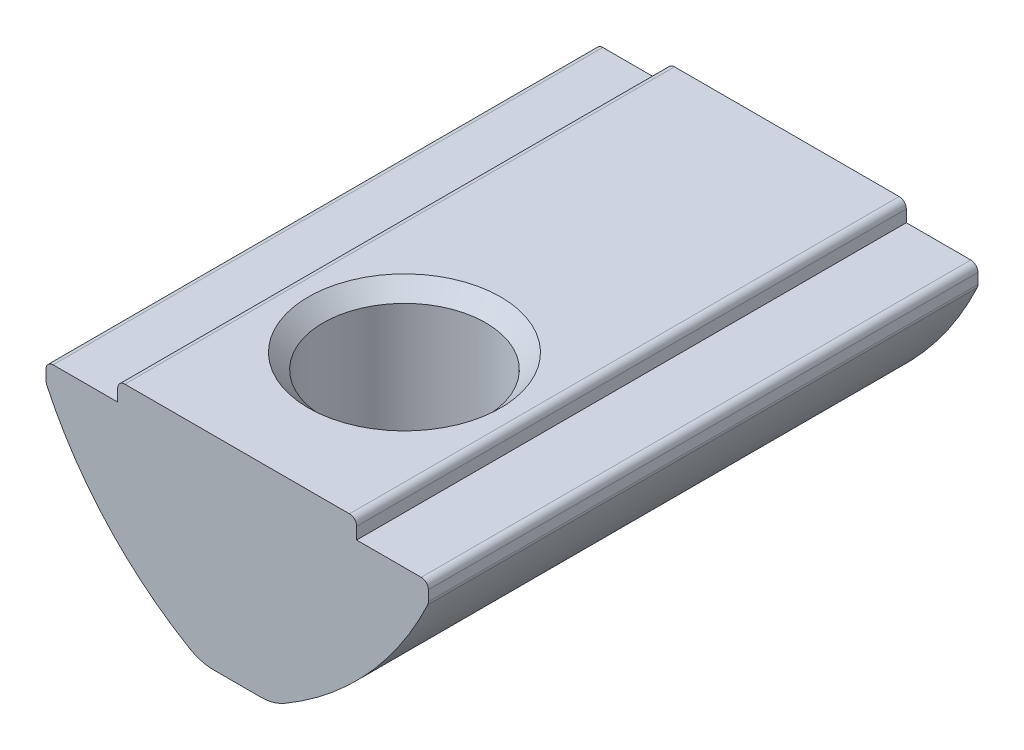
SolidWorks part; units mm, degrees
ref_plane "Спереди" through (0, 0, 0) normal (0, 0, 1) x (1, 0, 0)
ref_plane "Сверху" through (0, 0, 0) normal (0, 1, 0) x (1, 0, 0)
ref_plane "Справа" through (0, 0, 0) normal (1, 0, 0) x (0, 0, -1)
sketch "Эскиз1" plane through (0, 0, 0) normal (0, 0, 1) x (1, 0, 0)
  line L0 (-5, 0) -> (5, 0)
  line L5 (-5, 0) -> (-5, -0.8)
  line L6 (-5, -0.8) -> (-8, -0.8)
  line L7 (-8, -0.8) -> (-8, -1.6)
  line L8 (5, 0) -> (5, -0.8)
  line L9 (5, -0.8) -> (8, -0.8)
  line L10 (8, -0.8) -> (8, -1.6)
  line L11 (-1.5, -8.5) -> (1.5, -8.5)
  arc A0 (-8, -1.6) -> (-1.5, -8.5) centre (5.609, 4.7084) ccw
  arc A1 (1.5, -8.5) -> (8, -1.6) centre (-5.609, 4.7084) ccw
  point P0 (0, -8.5)
  point P4 (0, 0)
  dimension "D7" = 15
  dimension "D1" = 10
  dimension "D2" = 16
  dimension "D3" = 0.8
  dimension "D4" = 3
  dimension "D5" = 0.8
  dimension "D6" = 8.5
extrude "Бобышка-Вытянуть1" add sketch "Эскиз1" along normal mid plane 23
fillet "Скругление1" radius 0.3 6 edges at (8, -1.6, 0) (8, -0.8, 0) (-8, -0.8, 0) (-8, -1.6, 0) (5, 0, 0) (-5, 0, 0)
fillet "Скругление2" radius 2 2 edges at (1.5, -8.5, 0) (-1.5, -8.5, 0)
hole_wizard "Отверстие обработанное метчиком M83" positions "Эскиз2" profile "Эскиз4" tap size "M8" standard "ISO" end condition through all
sketch "Эскиз2" plane through (0, 0, 0) normal (0, 1, 0) x (1, 0, 0)
  line L0 (4.7, -11.5) -> (-4.7, -11.5) construction
  point P0 (0, -4.5)
  dimension "D1" = 7
sketch "Эскиз4" plane through (0, 0, 4.5) normal (1, 0, 0) x (0, 0, 1)
  line L0 (0, 0) -> (0, 8.5)
  line L1 (0, 8.5) -> (3.4, 8.5)
  line L2 (3.4, 8.5) -> (3.4, 0.625)
  line L3 (3.4, 0.625) -> (4.025, 0)
  line L5 (4.025, 0) -> (0, 0)
  line L6 (-3.4, 0.625) -> (-4.025, 0) construction
  line L11 (0, -6.35) -> (0, 107.95) construction
  dimension "Диаметр проходного сверла" = 6.8
  dimension "Глубина проходного сверла" = 8.5
  dimension "Диаметр передней зенковки" = 8.05
  dimension "Угол передней зенковки" = 90
cosmetic thread "Отверстие резьбы1" parameters "D2"=8
sketch "Эскиз5" plane through (0, 0, 0) normal (1, 0, 0) x (0, 0, -1)
  line L1 (6.5, -4.3) -> (6.5, -9.3) construction
  line L2 (11.5, -8.2244) -> (11.5, -1.6609) construction
  line L3 (6.5, -4.3) -> (6.5, -9.3)
  line L5 (11.5, -8.5) -> (-1.2433, -8.5) construction
  arc A0 (6.5, -4.3) -> (6.5, -9.3) centre (6.5, -6.8) ccw
  point P3 (4, -7.4722)
  dimension "D3" = 2.5
  dimension "D1" = 0.8
  dimension "D2" = 5
revolve "Повернуть1" add sketch "Эскиз5" angle 360 about L1
